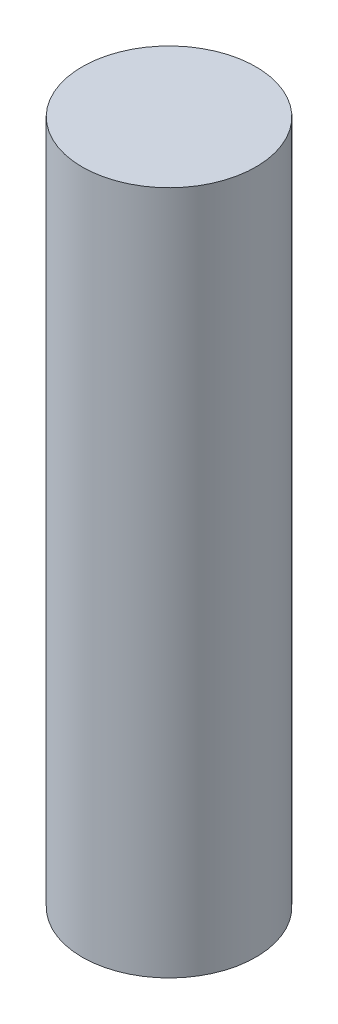
SolidWorks part; units mm, degrees
ref_plane "Front Plane" through (0, 0, 0) normal (0, 0, 1) x (1, 0, 0)
ref_plane "Top Plane" through (0, 0, 0) normal (0, 1, 0) x (1, 0, 0)
ref_plane "Right Plane" through (0, 0, 0) normal (1, 0, 0) x (0, 0, -1)
sketch "Sketch2" plane through (0, 0, 0) normal (0, 1, 0) x (1, 0, 0)
  circle A0 centre (0, 0) radius 12.5
  dimension "D1" = 25
extrude "Boss-Extrude1" add sketch "Sketch2" along normal blind 98.5
sketch "Sketch3" plane through (0, 0, 0) normal (0, -1, 0) x (1, 0, 0)
  circle A0 centre (0, 0) radius 3.175
  dimension "D1" = 6.35
extrude "Cut-Extrude1" cut sketch "Sketch3" against normal blind 10 contours A0
